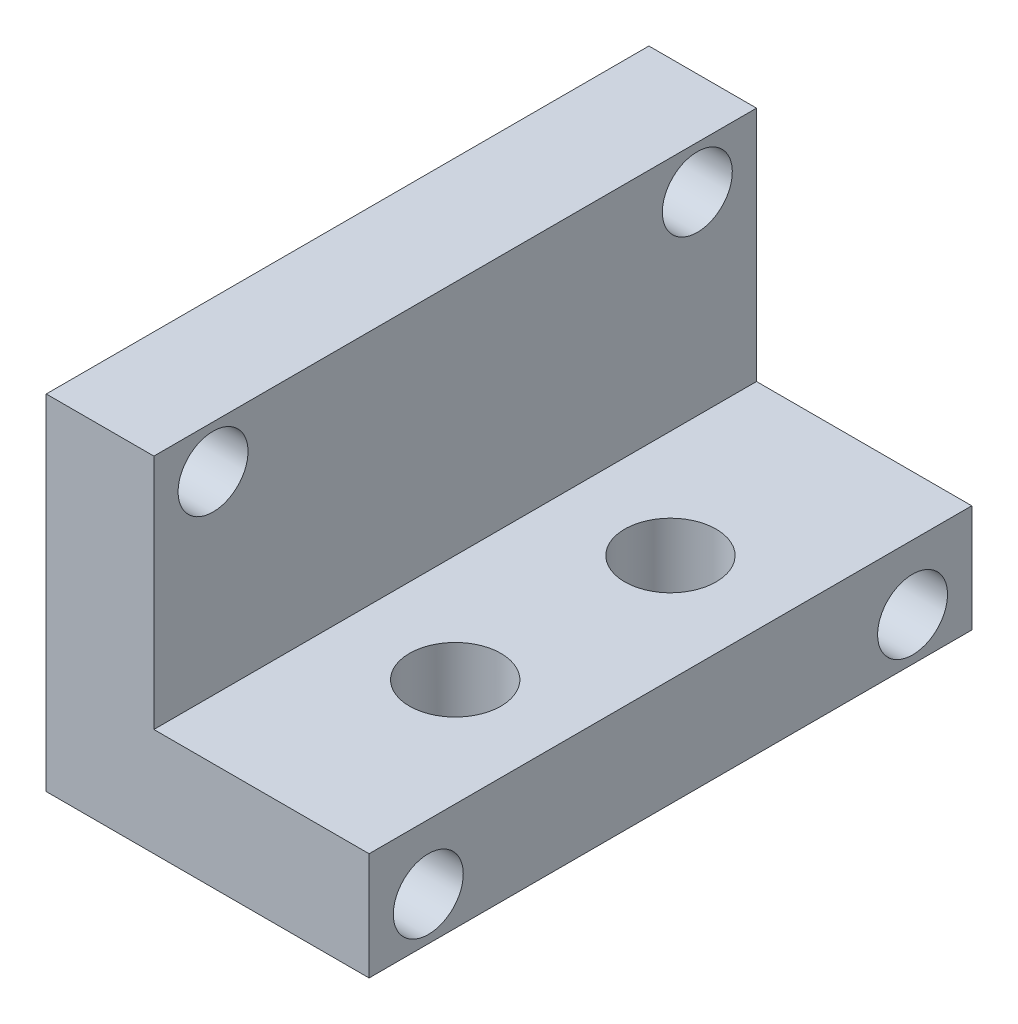
SolidWorks part; units mm, degrees
ref_plane "Plan de face" through (0, 0, 0) normal (0, 0, 1) x (1, 0, 0)
ref_plane "Plan de dessus" through (0, 0, 0) normal (0, 1, 0) x (1, 0, 0)
ref_plane "Plan de droite" through (0, 0, 0) normal (1, 0, 0) x (0, 0, -1)
sketch "Esquisse1" plane through (0, 0, 0) normal (0, 0, 1) x (1, 0, 0)
  line L0 (0, 0) -> (5, 0)
  line L1 (5, 0) -> (5, -11)
  line L2 (5, -11) -> (15, -11)
  line L3 (15, -11) -> (15, -16)
  line L4 (15, -16) -> (0, -16)
  line L5 (0, -16) -> (0, 0)
  dimension "D1" = 16
  dimension "D2" = 5
  dimension "D3" = 5
  dimension "D4" = 10
extrude "Boss.-Extru.1" add sketch "Esquisse1" along normal blind 28
sketch "Esquisse3" plane through (0, 0, 0) normal (-1, 0, 0) x (0, 0, 1)
  line L0 (14, 0) -> (14, -16) construction
  line L1 (28, 0) -> (0, 0) construction
  line L2 (28, -16) -> (0, -16) construction
  line L3 (0, -8) -> (28, -8) construction
  line L4 (0, 0) -> (0, -16) construction
  line L5 (28, 0) -> (28, -16) construction
  line L6 (25.25, -2) -> (25.25, -8) construction
  line L7 (2.75, -14) -> (2.75, -8) construction
  line L8 (25.25, -2) -> (14, -2) construction
  line L9 (2.75, -14) -> (14, -14) construction
  circle A0 centre (25.25, -2) radius 1.625
  circle A1 centre (2.75, -14) radius 1.625
  circle A2 centre (25.25, -14) radius 1.625
  circle A3 centre (2.75, -2) radius 1.625
  dimension "D1" = 3.25
  dimension "D2" = 3.25
  dimension "D3" = 22.5
  dimension "D4" = 12
extrude "Enlèv. mat.-Extru.1" cut sketch "Esquisse3" against normal through all
sketch "Esquisse4" plane through (0, -11, 0) normal (0, 1, 0) x (1, 0, 0)
  line L0 (5, -14) -> (15, -14) construction
  line L1 (5, -28) -> (5, 0) construction
  line L2 (15, -28) -> (15, 0) construction
  circle A0 centre (10, -9) radius 2.125
  circle A1 centre (10, -19) radius 2.125
  dimension "D1" = 4.25
  dimension "D2" = 5
  dimension "D3" = 5
extrude "Enlèv. mat.-Extru.2" cut sketch "Esquisse4" against normal blind 10
